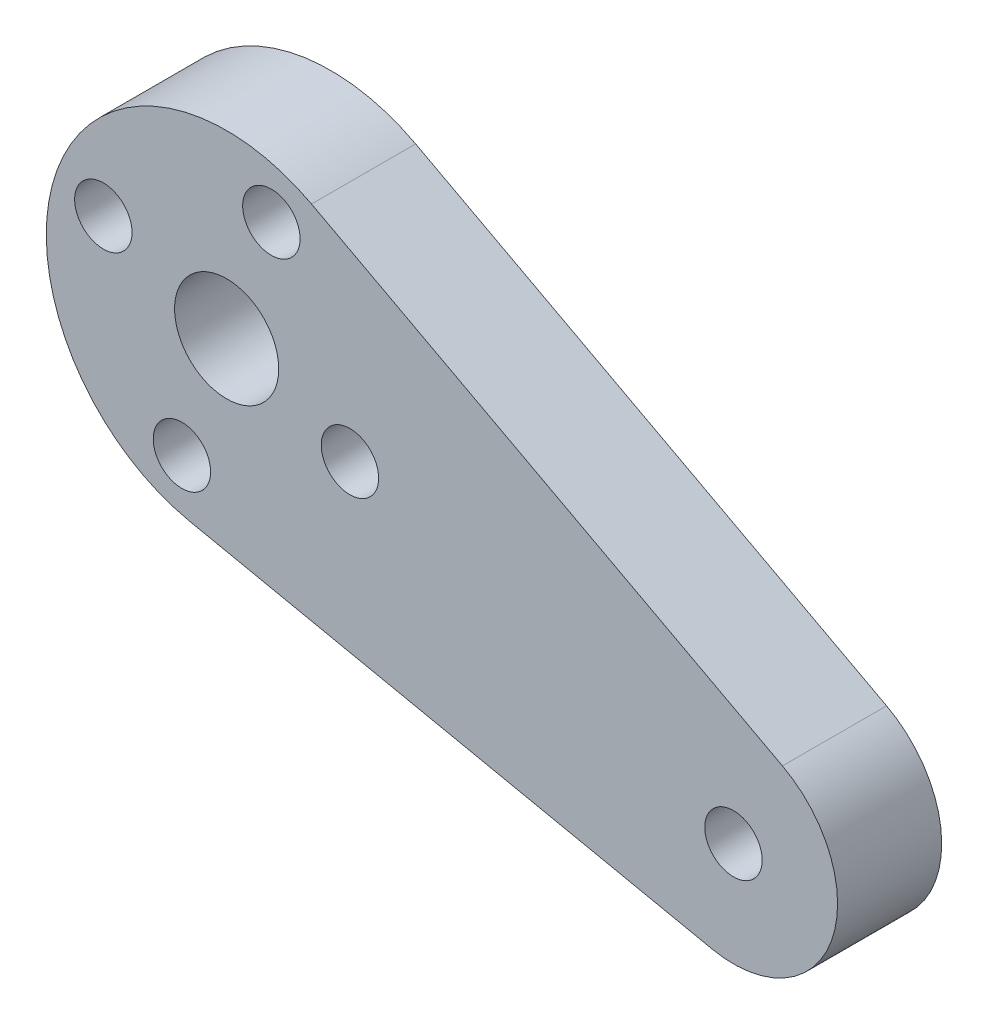
SolidWorks part; units mm, degrees
ref_plane "Front Plane" through (0, 0, 0) normal (0, 0, 1) x (1, 0, 0)
ref_plane "Top Plane" through (0, 0, 0) normal (0, 1, 0) x (1, 0, 0)
ref_plane "Right Plane" through (0, 0, 0) normal (1, 0, 0) x (0, 0, -1)
sketch "Sketch3" plane through (0, 0, 0) normal (0, 0, 1) x (1, 0, 0)
  line L0 (0, 0) -> (40.3547, 419.1) construction
  line L1 (40.3547, 419.1) -> (159.2585, 419.1) construction
  line L2 (159.2585, 419.1) -> (159.2585, 0) construction
  line L3 (159.2585, 0) -> (0, 0) construction
  line L4 (159.2585, -1000) -> (159.2585, 49000) construction
  line L5 (2.0164, 20.9415) -> (40.3547, 419.1) construction
  line L6 (2.0164, 20.9415) -> (41.8323, 17.1077) construction
  line L7 (40.3547, 419.1) -> (80.1706, 415.2662) construction
  line L8 (41.8323, 17.1077) -> (80.1706, 415.2662) construction
  line L9 (64.0085, -1000) -> (64.0085, 49000) construction
  line L10 (-42.7214, 317.5) -> (-118.5706, 324.8034) construction
  line L11 (-20.0013, 414.3375) -> (40.196, 414.3375) construction
  line L12 (-1162.1335, 304.8) -> (48837.8665, 304.8) construction
  line L13 (-120.1415, 292.1) -> (-43.9415, 292.1) construction
  line L14 (-118.5706, 324.8034) -> (-43.9415, 292.1) construction
  line L15 (-42.7214, 317.5) -> (-120.1415, 292.1) construction
  line L16 (40.196, 338.1375) -> (-20.0013, 338.1375) construction
  line L17 (-128.0517, 325.7164) -> (29.8985, 310.5075)
  line L18 (-128.0517, 325.7164) -> (-127.4431, 332.0371)
  line L19 (-127.4431, 332.0371) -> (40.3547, 419.1)
  line L20 (40.3547, 419.1) -> (100.3991, 419.1)
  line L21 (108.4585, 419.1) -> (108.4585, 0) construction
  line L22 (29.8985, 310.5075) -> (0.4102, 4.2603)
  line L23 (0.4102, 4.2603) -> (44.6556, 0)
  line L24 (44.6556, 0) -> (108.4585, 0)
  line L25 (111.8902, 411.8076) -> (159.2585, 311.15)
  line L26 (159.2585, 311.15) -> (159.2585, 304.8)
  line L27 (159.2585, 304.8) -> (108.4585, 280.8941)
  line L28 (108.4585, 280.8941) -> (108.4585, 0)
  line L29 (100.3991, 406.4) -> (28627.168, -40334.0482) construction
  line L30 (107.4945, 405.1489) -> (48105.9225, -8058.269) construction
  line L31 (46.2285, 266.7) -> (77.1396, 255.4859) construction
  line L32 (46.2285, 266.7) -> (77.1396, 277.9141) construction
  line L33 (114.9679, 385.5935) -> (125.3711, 392.878) construction
  line L34 (125.4132, 401.9893) -> (127.6185, 414.4964) construction
  line L35 (77.1396, 277.9141) -> (127.6185, 414.4964) construction
  line L36 (125.3711, 392.878) -> (77.1396, 255.4859) construction
  line L37 (77.1396, 277.9141) -> (64.0085, 277.9141) construction
  line L38 (77.1396, 255.4859) -> (64.0085, 255.4859) construction
  arc A0 (-118.5706, 324.8034) -> (-20.0013, 414.3375) centre (-20.0013, 315.3123) cw construction
  arc A1 (73.5335, 304.8) -> (40.196, 338.1375) centre (40.196, 304.8) ccw construction
  arc A2 (149.7335, 304.8) -> (40.196, 414.3375) centre (40.196, 304.8) ccw construction
  arc A3 (-42.7214, 317.5) -> (-20.0013, 338.1375) centre (-20.0013, 315.3123) cw construction
  arc A4 (100.3991, 419.1) -> (111.8902, 411.8076) centre (100.3991, 406.4) cw
  point P7 (57.6585, 400.05)
  point P17 (149.7335, 304.8)
  point P18 (73.5335, 304.8)
  dimension "D9" = 9.525
  dimension "D14" = 25.4
  dimension "D22" = 12.7
  dimension "D1" = 419.1
  dimension "D2" = 101.6
  dimension "D3" = 19.05
  dimension "D4" = 19.05
  dimension "D5" = 84.5
  dimension "D6" = 40
  dimension "D7" = 400
  dimension "D8" = 95.25
  dimension "D10" = 9.525
  dimension "D11" = 114.3
  dimension "D12" = 76.2
  dimension "D13" = 9.525
  dimension "D15" = 127
  dimension "D16" = 9.525
  dimension "D17" = 203.2
  dimension "D18" = 6.35
  dimension "D19" = 50.8
  dimension "D20" = 44.45
  dimension "D21" = 6.35
  dimension "D23" = 55
  dimension "D24" = 25.4
  dimension "D25" = 12.7
  dimension "D26" = 25.4
  dimension "D27" = 12.7
  dimension "D28" = 17.78
  dimension "D29" = 38.1
  dimension "D30" = 39.88
  dimension "D31" = 10
sketch "Sketch4" plane through (0, 0, 0) normal (0, 0, 1) x (1, 0, 0)
  line L0 (43.9771, 255.9329) -> (75.84, 249.2704)
  line L1 (51.4045, 276.4061) -> (80.1276, 261.089)
  line L2 (46.2285, 266.7) -> (77.1396, 255.4859) construction
  arc A0 (51.4045, 276.4061) -> (43.9771, 255.9329) centre (46.2285, 266.7) ccw
  arc A1 (75.84, 249.2704) -> (80.1276, 261.089) centre (77.1396, 255.4859) ccw
  circle A2 centre (46.2285, 266.7) radius 3.175
  circle A3 centre (53.7489, 263.9717) radius 1.75
  circle A4 centre (77.1396, 255.4859) radius 1.75
  circle A5 centre (43.5003, 259.1796) radius 1.75
  circle A6 centre (38.7081, 269.4283) radius 1.75
  circle A7 centre (48.9568, 274.2204) radius 1.75
  point P23 (46.2285, 266.7)
  dimension "D1" = 11
  dimension "D2" = 6.35
  dimension "D3" = 3.5
  dimension "D4" = 6.35
  dimension "D5" = 8
  dimension "D6" = 4
extrude "Boss-Extrude1" add sketch "Sketch4" along normal blind 6.35
